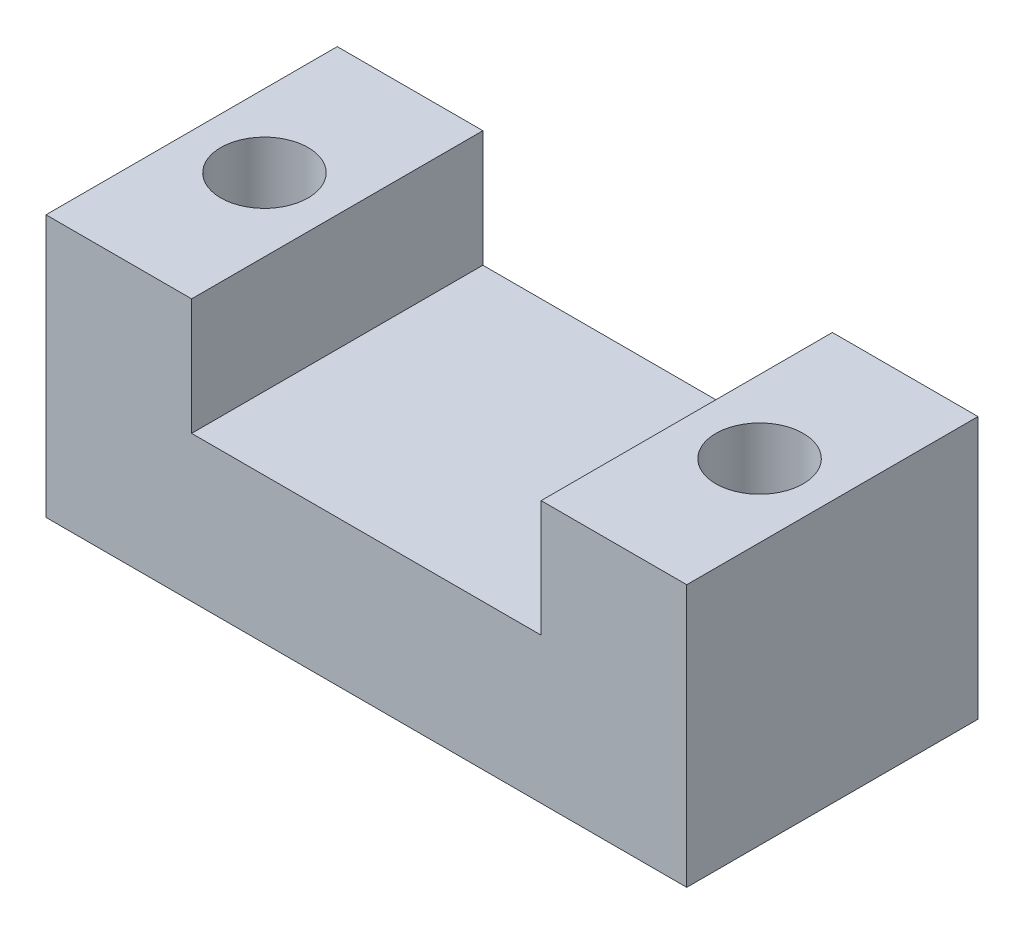
SolidWorks part; units mm, degrees
ref_plane "前基準面" through (0, 0, 0) normal (0, 0, 1) x (1, 0, 0)
ref_plane "上基準面" through (0, 0, 0) normal (0, 1, 0) x (1, 0, 0)
ref_plane "右基準面" through (0, 0, 0) normal (1, 0, 0) x (0, 0, -1)
sketch "草圖1" plane through (0, 0, 0) normal (0, 1, 0) x (1, 0, 0)
  line L0 (-8.5, 0) -> (8.5, 0) construction
  line L1 (-11, -5) -> (11, -5)
  line L2 (-11, -5) -> (-11, 5)
  line L3 (-11, 5) -> (11, 5)
  line L4 (11, -5) -> (11, 5)
  line L5 (-11, -5) -> (11, 5) construction
  line L6 (-11, 5) -> (11, -5) construction
  circle A0 centre (-8.5, 0) radius 1.5
  circle A1 centre (8.5, 0) radius 1.5
  point P0 (0, 0)
  dimension "D4" = 3
  dimension "D1" = 22
  dimension "D2" = 10
  dimension "D3" = 17
extrude "填料-伸長1" add sketch "草圖1" along normal blind 5
sketch "草圖2" plane through (0, 5, 0) normal (0, 1, 0) x (1, 0, 0)
  line L0 (-11, -5) -> (11, -5) construction
  line L1 (-11, 5) -> (-6, 5)
  line L2 (-11, 5) -> (-11, -5)
  line L3 (-11, -5) -> (-6, -5)
  line L4 (-6, 5) -> (-6, -5)
  line L6 (11, 5) -> (6, 5)
  line L7 (11, 5) -> (11, -5)
  line L8 (11, -5) -> (6, -5)
  line L9 (6, 5) -> (6, -5)
  circle A0 centre (8.5, 0) radius 1.5 construction
  circle A1 centre (-8.5, 0) radius 1.5 construction
  circle A2 centre (8.5, 0) radius 1.5
  circle A3 centre (-8.5, 0) radius 1.5
  dimension "D1" = 5
  dimension "D2" = 12
extrude "填料-伸長2" add sketch "草圖2" along normal blind 4
